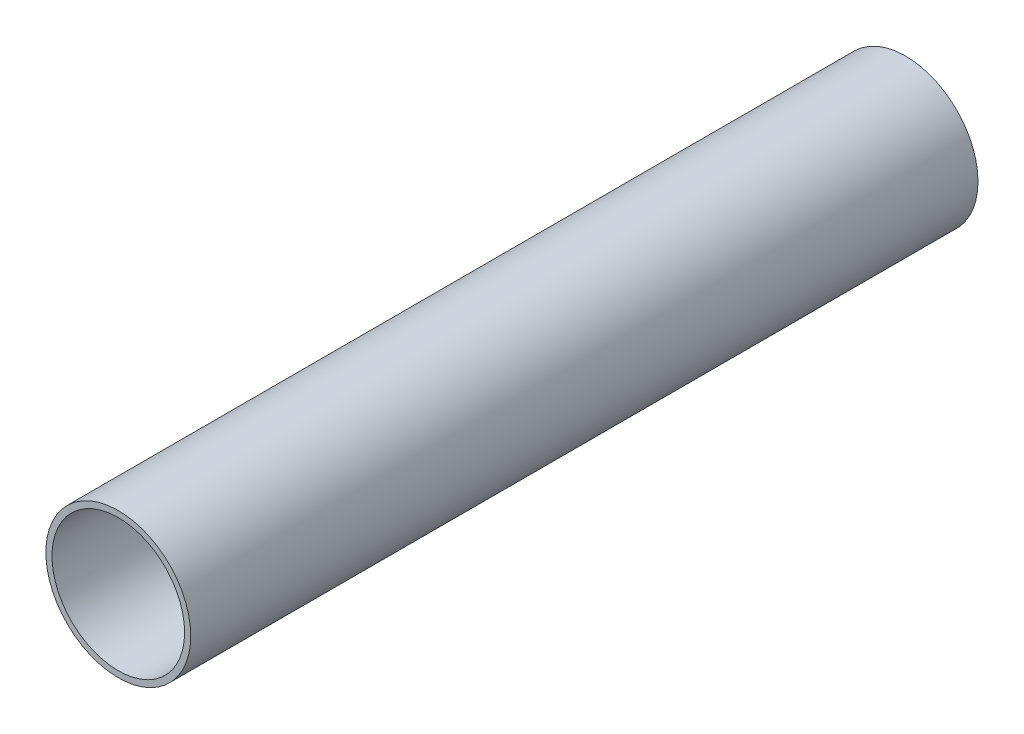
SolidWorks part; units mm, degrees
ref_plane "Front Plane" through (0, 0, 0) normal (0, 0, 1) x (1, 0, 0)
ref_plane "Top Plane" through (0, 0, 0) normal (0, 1, 0) x (1, 0, 0)
ref_plane "Right Plane" through (0, 0, 0) normal (1, 0, 0) x (0, 0, -1)
sketch "Sketch1" plane through (0, 0, 0) normal (0, 0, 1) x (1, 0, 0)
  circle A0 centre (0, 0) radius 84.1375
  dimension "Pipe OD" = 168.275
extrude "Extrude-Thin1" add sketch "Sketch1" along normal mid plane 914.4 thin thin type one direction reverse wall 7.112
